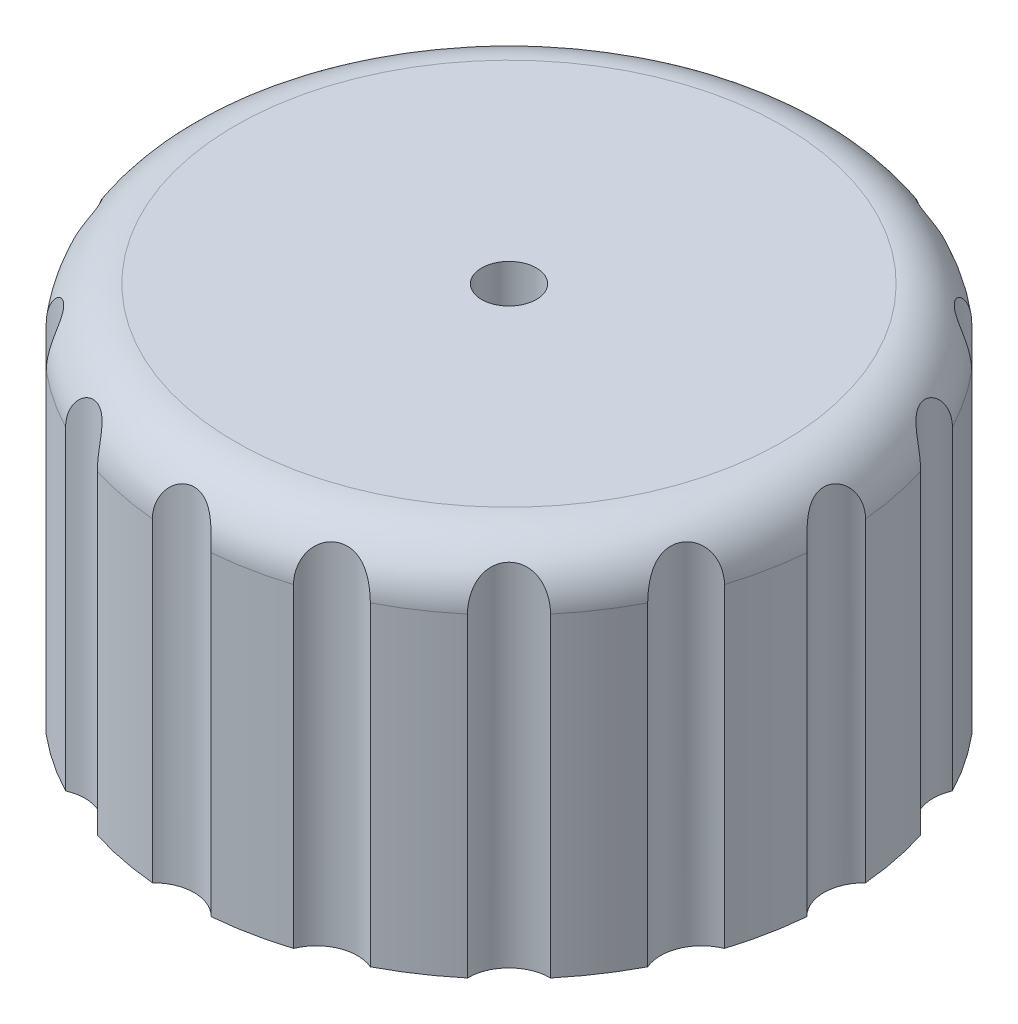
SolidWorks part; units mm, degrees
ref_plane "Front Plane" through (0, 0, 0) normal (0, 0, 1) x (1, 0, 0)
ref_plane "Top Plane" through (0, 0, 0) normal (0, 1, 0) x (1, 0, 0)
ref_plane "Right Plane" through (0, 0, 0) normal (1, 0, 0) x (0, 0, -1)
sketch "Sketch1" plane through (0, 0, 0) normal (0, 0, 1) x (1, 0, 0)
  line L0 (-2.765, 0) -> (-2.765, 2.8911)
  line L1 (-2.765, 2.8911) -> (0, 2.8911)
  line L2 (0, 2.8911) -> (0, 8)
  line L3 (0, 8) -> (-6, 8)
  line L4 (-6, 8) -> (-6, 1.2448)
  line L5 (-6, 1.2448) -> (-4.0034, 1.2448)
  line L6 (-4.0034, 1.2448) -> (-3.0676, 0)
  line L7 (-3.0676, 0) -> (-2.765, 0)
  dimension "D1" = 2.765
  dimension "D2" = 6
  dimension "D3" = 8
revolve "Revolve1" add sketch "Sketch1" angle 360 about L2
fillet "Fillet1" radius 1 1 edges at (0, 8, -6)
sketch "Sketch2" plane through (0, 0, 0) normal (0, 1, 0) x (1, 0, 0)
  circle A0 centre (0, 6.5) radius 0.75
  dimension "D2" = 1.5
  dimension "D1" = 6.5
extrude "Cut-Extrude1" cut sketch "Sketch2" along normal through all
pattern_circular "CirPattern1" count 16 over 360 about axis through (0, 0, 0) along (0, 1, 0) of "Cut-Extrude1"
sketch "Sketch3" plane through (0, 0, 0) normal (0, 1, 0) x (1, 0, 0)
  circle A0 centre (0, 0) radius 0.5
extrude "Cut-Extrude2" cut sketch "Sketch3" along normal through all
